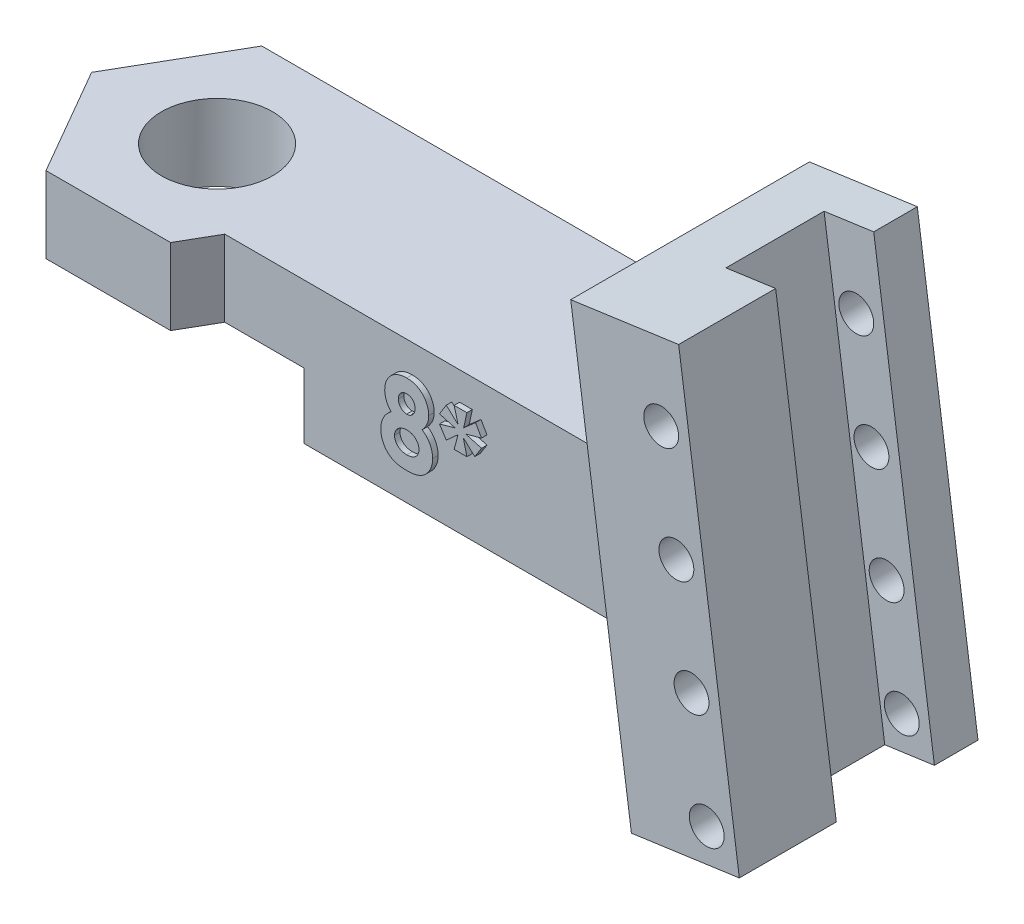
SolidWorks part; units mm, degrees
ref_plane "Front Plane" through (0, 0, 0) normal (0, 0, 1) x (1, 0, 0)
ref_plane "Top Plane" through (0, 0, 0) normal (0, 1, 0) x (1, 0, 0)
ref_plane "Right Plane" through (0, 0, 0) normal (1, 0, 0) x (0, 0, -1)
sketch "Sketch1" plane through (0, 0, 0) normal (0, 1, 0) x (1, 0, 0)
  line L1 (0, 0) -> (25, 0)
  line L2 (0, 0) -> (0, -6.75)
  line L3 (0, -6.75) -> (25, -6.75)
  line L4 (25, 0) -> (25, -6.75)
  dimension "D1" = 6.75
  dimension "D2" = 25
extrude "Boss-Extrude1" add sketch "Sketch1" along normal blind 6.5
ref_plane "Plane1" through (0, 0, 3.375) normal (0, 0, 1) x (1, 0, 0)
sketch "Sketch5" plane through (0, 6.5, 0) normal (0, 1, 0) x (1, 0, 0)
  line L0 (0, 0) -> (0, -6.75) construction
  line L1 (-5.7158, -3.375) -> (-2.8579, -8.325)
  line L2 (-2.8579, -8.325) -> (2.8579, -8.325)
  line L3 (2.8579, -8.325) -> (5.7158, -3.375)
  line L4 (5.7158, -3.375) -> (2.8579, 1.575)
  line L5 (2.8579, 1.575) -> (-2.8579, 1.575)
  line L6 (-2.8579, 1.575) -> (-5.7158, -3.375)
  circle A0 centre (0, -3.375) radius 4.95 construction
  dimension "D1" = 4.95
extrude "Boss-Extrude4" add sketch "Sketch5" against normal up to surface (6.5 mm away) up to face at (12.5, 0, 3.375)
sketch "Sketch3" plane through (0, 0, 3.375) normal (0, 0, 1) x (1, 0, 0)
  line L0 (22.2652, 14.4574) -> (27.2165, 15.1533)
  line L1 (27.2165, 15.1533) -> (30, -4.6521)
  line L2 (30, -4.6521) -> (25.0487, -5.3479)
  line L3 (25.0487, -5.3479) -> (22.2652, 14.4574)
  line L4 (3.7672, 6.5) -> (25, 6.5) construction
  point P6 (27.5243, -5)
  dimension "D1" = 30
  dimension "D2" = 5
  dimension "D3" = 20
  dimension "D4" = 82
  dimension "D6" = 5
extrude "Boss-Extrude3" add sketch "Sketch3" against normal up to surface (4.95 mm away) and the other way blind 6 up to face at (0, 3.25, -1.575)
sketch "Sketch4" plane through (-1.5612, 11.1088, 0) normal (-0.1392, 0.9903, 0) x (0.9903, 0.1392, 0)
  line L0 (29.0606, -9.375) -> (29.0606, 1.575) construction
  line L1 (26.7606, -0.425) -> (29.0606, -0.425)
  line L2 (26.7606, -0.425) -> (26.7606, -4.925)
  line L3 (26.7606, -4.925) -> (29.0606, -4.925)
  line L4 (29.0606, -0.425) -> (29.0606, -4.925)
  line L6 (29.0606, 1.575) -> (24.0606, 1.575) construction
  dimension "D1" = 4.5
  dimension "D2" = 2.3
  dimension "D3" = 2
extrude "Cut-Extrude1" cut sketch "Sketch4" against normal blind 23 contours L2 L3 L4 L1
sketch "Sketch6" plane through (0, 6.5, 0) normal (0, 1, 0) x (1, 0, 0)
  circle A0 centre (0, -3.3356) radius 2.55
  dimension "D1" = 5.1
extrude "Cut-Extrude2" cut sketch "Sketch6" against normal blind 10
sketch "Sketch7" plane through (0, 0, -1.575) normal (0, 0, -1) x (-1, 0, 0)
  line L0 (-2.8579, 0) -> (-24.2971, 0)
  line L1 (-24.2971, 0) -> (-25.0487, -5.3479)
  line L2 (-25.0487, -5.3479) -> (-30, -4.6521)
  line L3 (-30, -4.6521) -> (-27.2165, 15.1533)
  line L4 (-27.2165, 15.1533) -> (-22.2652, 14.4574)
  line L5 (-22.2652, 14.4574) -> (-23.3835, 6.5)
  line L6 (-23.3835, 6.5) -> (-2.8579, 6.5)
  line L7 (-2.8579, 6.5) -> (-2.8579, 0)
  dimension "D1" = 20
extrude "Boss-Extrude5" add sketch "Sketch7" against normal up to surface (1.575 mm away) up to face at (13.8038, 3.25, 0)
sketch "Sketch8" plane through (0, 0, 0) normal (0, -1, 0) x (-1, 0, 0)
  line L1 (-4.6765, -11.475) -> (4.6765, -11.475)
  line L2 (4.6765, -11.475) -> (9.3531, -3.375)
  line L3 (9.3531, -3.375) -> (4.6765, 4.725)
  line L4 (4.6765, 4.725) -> (-4.6765, 4.725)
  line L5 (-4.6765, 4.725) -> (-9.3531, -3.375)
  line L6 (-9.3531, -3.375) -> (-4.6765, -11.475)
  circle A0 centre (0, -3.375) radius 8.1 construction
  dimension "D1" = 16.2
extrude "Cut-Extrude3" cut sketch "Sketch8" against normal blind 3
sketch "Sketch9" plane through (0, 0, -1.575) normal (0, 0, -1) x (-1, 0, 0)
  line L0 (-30, -4.6521) -> (-27.2165, 15.1533) construction
  line L1 (-25.0487, -5.3479) -> (-30, -4.6521) construction
  line L2 (-28.5039, -3.3476) -> (-26.4163, 11.5064) construction
  line L3 (-30, -4.6521) -> (-27.2165, 15.1533) construction
  circle A0 centre (-28.5039, -3.3476) radius 0.8
  circle A4 centre (-27.808, 1.6038) radius 0.8
  circle A5 centre (-27.1122, 6.5551) radius 0.8
  circle A6 centre (-26.4163, 11.5064) radius 0.8
  dimension "D1" = 1.6
  dimension "D2" = 1.3
  dimension "D5" = 5
  dimension "D3" = 1.5
  dimension "D4" = 5
  dimension "D6" = 5
extrude "Cut-Extrude4" cut sketch "Sketch9" against normal up to surface (10.95 mm away) up to face at (26.1326, 4.9027, 9.375)
sketch "Sketch10" plane through (0, 0, 6.75) normal (0, 0, 1) x (1, 0, 0)
  text T0 "<b>8*</b>"
extrude "Boss-Extrude6" add sketch "Sketch10" along normal blind 0.25
